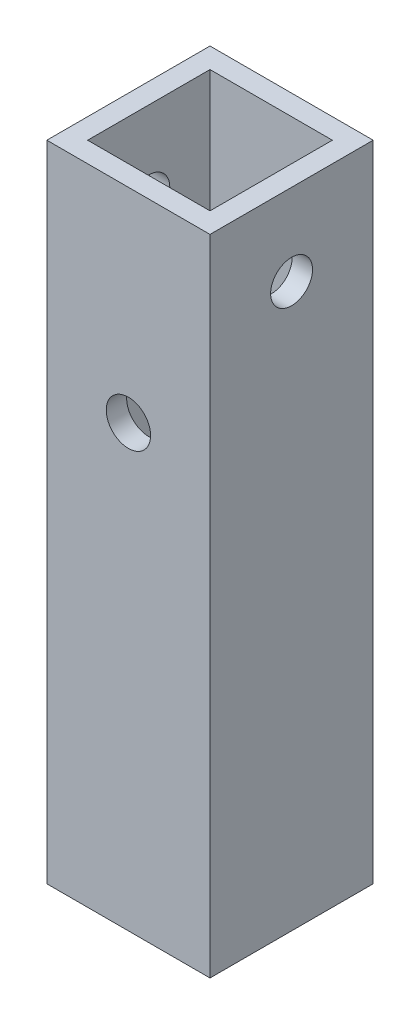
SolidWorks part; units mm, degrees
ref_plane "Front Plane" through (0, 0, 0) normal (0, 0, 1) x (1, 0, 0)
ref_plane "Top Plane" through (0, 0, 0) normal (0, 1, 0) x (1, 0, 0)
ref_plane "Right Plane" through (0, 0, 0) normal (1, 0, 0) x (0, 0, -1)
sketch "Sketch1" plane through (0, 0, 0) normal (0, 1, 0) x (1, 0, 0)
  line L0 (9.525, 9.525) -> (-9.525, 9.525)
  line L1 (12.7, -12.7) -> (-12.7, -12.7)
  line L2 (12.7, -12.7) -> (12.7, 12.7)
  line L3 (12.7, 12.7) -> (-12.7, 12.7)
  line L4 (-12.7, -12.7) -> (-12.7, 12.7)
  line L5 (12.7, -12.7) -> (-12.7, 12.7) construction
  line L6 (12.7, 12.7) -> (-12.7, -12.7) construction
  line L7 (-9.525, -9.525) -> (-9.525, 9.525)
  line L8 (9.525, -9.525) -> (-9.525, -9.525)
  line L9 (9.525, -9.525) -> (9.525, 9.525)
  point P0 (0, 0)
  dimension "D1" = 25.4
  dimension "D2" = 25.4
  dimension "D3" = 3.175
extrude "Boss-Extrude1" add sketch "Sketch1" along normal blind 100.2538
hole_wizard "F (0.257) Diameter Hole1" positions "Sketch2" profile "Sketch3" hole size "F" standard "ANSI Inch" end condition through all
sketch "Sketch2" plane through (12.7, 0, 0) normal (1, 0, 0) x (0, 0, -1)
  line L0 (-12.7, 100.2538) -> (12.7, 100.2538) construction
  point P0 (0, 87.5538)
  dimension "D1" = 12.7
sketch "Sketch3" plane through (12.7, 87.5538, 0) normal (0, 1, 0) x (0, 0, -1)
  line L0 (0, 0) -> (0, 25.4)
  line L1 (0, 25.4) -> (3.2639, 25.4)
  line L2 (3.2639, 25.4) -> (3.2639, 0)
  line L5 (3.2639, 0) -> (0, 0)
  line L11 (0, -6.35) -> (0, 107.95) construction
  dimension "Thru Hole Dia." = 6.5278
  dimension "Thru Hole Depth" = 25.4
hole_wizard "I (0.272) Diameter Hole1" positions "Sketch4" profile "Sketch5" hole size "I" standard "ANSI Inch" end condition through all
sketch "Sketch4" plane through (0, 0, 12.7) normal (0, 0, 1) x (1, 0, 0)
  line L0 (-12.7, 100.2538) -> (12.7, 100.2538) construction
  point P0 (0, 68.5038)
  dimension "D1" = 31.75
sketch "Sketch5" plane through (0, 68.5038, 12.7) normal (1, 0, 0) x (0, -1, 0)
  line L0 (0, 0) -> (0, 25.4)
  line L1 (0, 25.4) -> (3.4544, 25.4)
  line L2 (3.4544, 25.4) -> (3.4544, 0)
  line L5 (3.4544, 0) -> (0, 0)
  line L11 (0, -6.35) -> (0, 107.95) construction
  dimension "Thru Hole Dia." = 6.9088
  dimension "Thru Hole Depth" = 25.4
